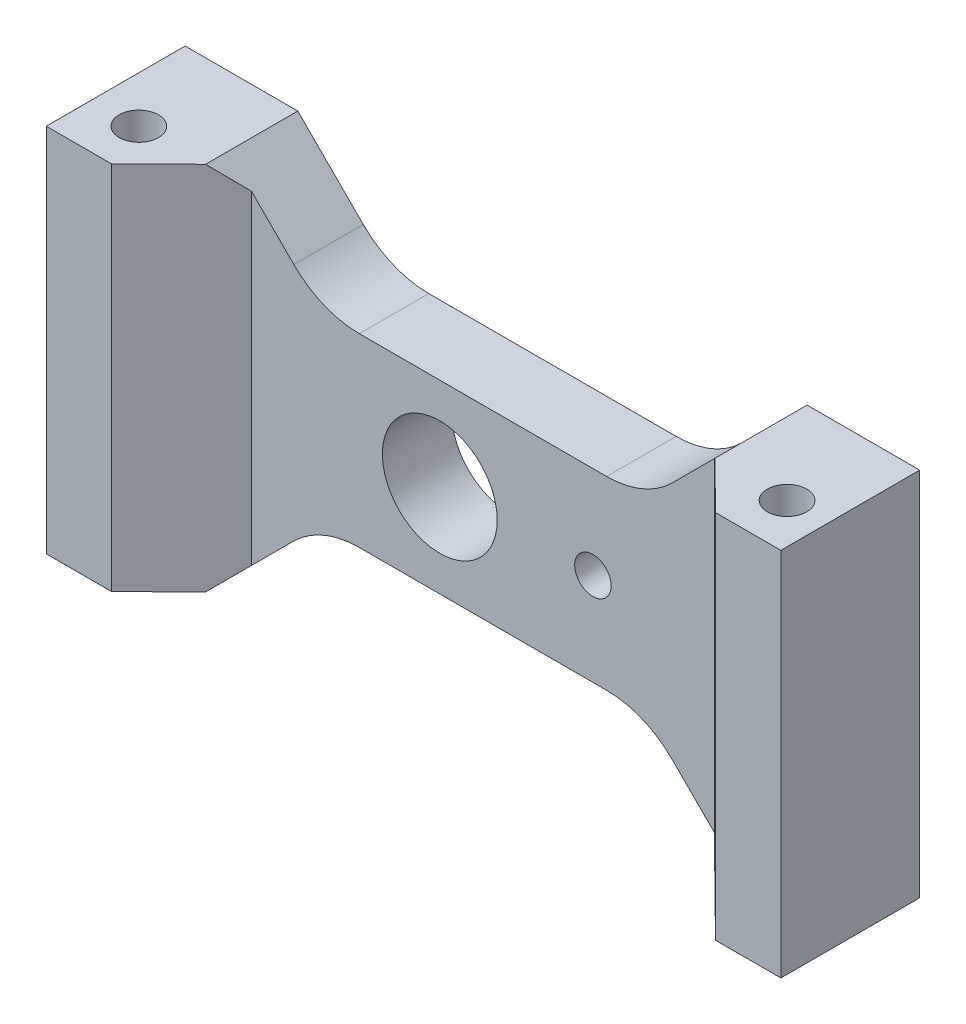
SolidWorks part; units mm, degrees
material "PET"
ref_plane "Front" through (0, 0, 0) normal (0, 0, 1) x (1, 0, 0)
ref_plane "Top" through (0, 0, 0) normal (0, 1, 0) x (1, 0, 0)
ref_plane "Right" through (0, 0, 0) normal (1, 0, 0) x (0, 0, -1)
sketch "Sketch1" plane through (0, 0, 0) normal (0, 1, 0) x (1, 0, 0)
  line L0 (25.1873, 0) -> (-25.1873, 0)
  line L1 (-25.1873, 0) -> (-25.1873, -9.525)
  line L2 (-25.1873, -9.525) -> (-20.7115, -9.525)
  line L3 (-20.7115, -9.525) -> (-15.875, -4.7625)
  line L4 (-15.875, -4.7625) -> (15.875, -4.7625)
  line L5 (15.875, -4.7625) -> (20.7115, -9.525)
  line L6 (20.7115, -9.525) -> (25.1873, -9.525)
  line L7 (25.1873, -9.525) -> (25.1873, 0)
  line L9 (22.4377, -6.35) -> (25.1873, -4.7625) construction
  line L10 (-22.0123, -6.35) -> (-25.1873, -6.35) construction
  line L11 (-22.0123, -6.35) -> (-19.7846, -8.6123) construction
  circle A0 centre (-22.0123, -6.35) radius 1.3526
  circle A1 centre (22.4377, -6.35) radius 1.3526
  point P3 (-14.2527, -9.525)
  point P4 (0, 0)
  point P17 (0, 0)
  dimension "D3" = 2.7051
  dimension "D4" = 44.45
  dimension "D2" = 3.175
  dimension "D7" = 6.35
  dimension "D1" = 9.525
  dimension "D5" = 4.7625
  dimension "D6" = 31.75
extrude "Boss-Extrude1" add sketch "Sketch1" along normal blind 25.4
sketch "Sketch2" plane through (0, 0, 4.7625) normal (0, 0, 1) x (1, 0, 0)
  line L0 (-2.9623, 25.4) -> (-2.9623, 0) construction
  line L1 (-15.875, 25.4) -> (15.875, 25.4) construction
  line L2 (-15.875, 0) -> (15.875, 0) construction
  line L3 (-25.1873, 25.4) -> (-25.1873, 0) construction
  circle A0 centre (-2.9623, 12.7) radius 3.937
  point P8 (0, 0)
  point P9 (-4.8478, 12.7)
  dimension "D1" = 7.874
  dimension "D2" = 22.225
extrude "Cut-Extrude1" cut sketch "Sketch2" against normal through all
sketch "Sketch5" plane through (0, 0, 4.7625) normal (0, 0, 1) x (1, 0, 0)
  line L0 (-4.5498, 12.7) -> (5.9502, 12.7) construction
  circle A0 centre (-2.9623, 12.7) radius 3.937 construction
  point P0 (7.5377, 12.7)
  dimension "D1" = 10.5
hole_wizard "M3x0.5 Tapped Hole1" positions "Sketch5" profile "Sketch4" tap size "M3x0.5" standard "ANSI Metric" end condition up to next
sketch "Sketch4" plane through (7.5377, 12.7, 4.7625) normal (1, 0, 0) x (0, -1, 0)
  line L0 (0, 0) -> (0, 4.7625)
  line L1 (0, 4.7625) -> (1.25, 4.7625)
  line L2 (1.25, 4.7625) -> (1.25, 0)
  line L5 (1.25, 0) -> (0, 0)
  line L11 (0, -6.35) -> (0, 107.95) construction
  dimension "Thru Tap Drill Dia." = 2.5
  dimension "Thru Tap Drill Depth" = 4.7625
cosmetic thread "Hole Thread1" parameters "D2"=3
sketch "Sketch6" plane through (0, 0, 0) normal (0, 0, -1) x (-1, 0, 0)
  line L0 (-17.4625, 25.4) -> (-12.9724, 20.9099)
  line L1 (-25.1873, 25.4) -> (25.1873, 25.4) construction
  line L2 (-8.4822, 19.05) -> (8.4822, 19.05)
  line L3 (12.9724, 20.9099) -> (17.4625, 25.4)
  line L4 (-17.4625, 0) -> (-12.9724, 4.4901)
  line L5 (-25.1873, 0) -> (25.1873, 0) construction
  line L6 (-8.4822, 6.35) -> (8.4822, 6.35)
  line L7 (12.9724, 4.4901) -> (17.4625, 0)
  line L8 (17.4625, 0) -> (-17.4625, 0)
  line L9 (-17.4625, 25.4) -> (17.4625, 25.4)
  line L10 (-25.1873, 12.7) -> (-17.8644, 12.7) construction
  line L11 (-25.1873, 25.4) -> (-25.1873, 0) construction
  line L12 (-25.1873, 25.4) -> (-17.4625, 25.4) construction
  line L13 (17.4625, 25.4) -> (25.1873, 25.4) construction
  arc A0 (12.9724, 4.4901) -> (8.4822, 6.35) centre (8.4822, 0) ccw
  arc A1 (-12.9724, 4.4901) -> (-8.4822, 6.35) centre (-8.4822, 0) cw
  arc A2 (-8.4822, 19.05) -> (-12.9724, 20.9099) centre (-8.4822, 25.4) cw
  arc A3 (8.4822, 19.05) -> (12.9724, 20.9099) centre (8.4822, 25.4) ccw
  point P17 (0, 0)
  point P23 (11.1125, 6.35)
  point P26 (-11.1125, 6.35)
  point P29 (-11.1125, 19.05)
  point P32 (11.1125, 19.05)
  dimension "D4" = 6.35
  dimension "D1" = 12.7
  dimension "D2" = 45
  dimension "D3" = 34.925
extrude "Cut-Extrude2" cut sketch "Sketch6" against normal through all
